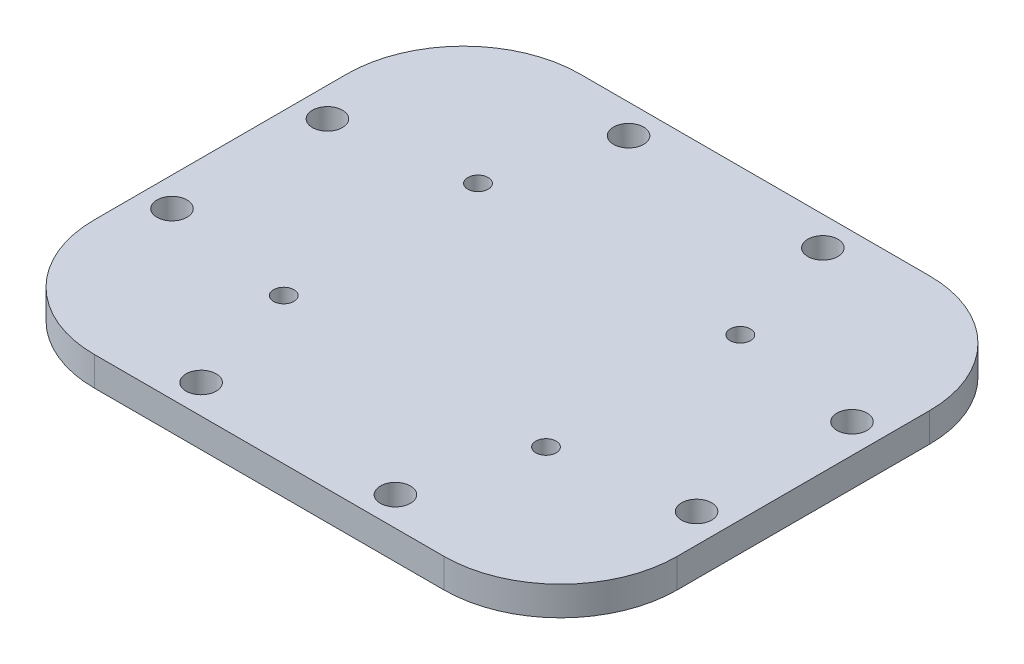
SolidWorks part; units mm, degrees
material "ABS"
ref_plane "前视基准面" through (0, 0, 0) normal (0, 0, 1) x (1, 0, 0)
ref_plane "上视基准面" through (0, 0, 0) normal (0, 1, 0) x (1, 0, 0)
ref_plane "右视基准面" through (0, 0, 0) normal (1, 0, 0) x (0, 0, -1)
other "Configuration Table"
sketch "草图1" plane through (0, 0, 0) normal (0, 1, 0) x (1, 0, 0)
  line L1 (-30, 25) -> (30, 25)
  line L2 (-30, 25) -> (-30, -25)
  line L3 (-30, -25) -> (30, -25)
  line L4 (30, 25) -> (30, -25)
  line L5 (-30, 25) -> (30, -25) construction
  line L6 (-30, -25) -> (30, 25) construction
  point P0 (0, 0)
  dimension "D1" = 60
  dimension "D2" = 50
extrude "凸台-拉伸1" add sketch "草图1" along normal blind 3
sketch "草图7" plane through (0, 3, 0) normal (0, 1, 0) x (1, 0, 0)
  line L0 (0, 0) -> (0, 25) construction
  line L1 (30, 25) -> (-30, 25) construction
  line L2 (0, 0) -> (30, 0) construction
  line L3 (30, -25) -> (30, 25) construction
  circle A0 centre (13.5, 10) radius 1.05
  circle A1 centre (-13.5, 10) radius 1.05
  circle A2 centre (-13.5, -10) radius 1.05
  circle A3 centre (13.5, -10) radius 1.05
  dimension "D1" = 2.1
  dimension "D2" = 20
  dimension "D3" = 27
extrude "切除-拉伸1" cut sketch "草图7" against normal blind 10
sketch "草图8" plane through (0, 0, 0) normal (0, -1, 0) x (1, 0, 0)
  line L0 (0, 25) -> (0, 0) construction
  line L1 (-30, 25) -> (30, 25) construction
  line L2 (0, 0) -> (30, 0) construction
  line L3 (30, 25) -> (30, -25) construction
  line L4 (-10, 22) -> (10, 22) construction
  circle A0 centre (27, 8) radius 1.55
  circle A1 centre (10, 22) radius 1.55
  circle A2 centre (-10, 22) radius 1.55
  circle A3 centre (-27, 8) radius 1.55
  circle A4 centre (-27, -8) radius 1.55
  circle A5 centre (-10, -22) radius 1.55
  circle A6 centre (10, -22) radius 1.55
  circle A7 centre (27, -8) radius 1.55
  dimension "D1" = 44
  dimension "D2" = 54
  dimension "D3" = 3.1
  dimension "D4" = 20
  dimension "D5" = 16
extrude "切除-拉伸2" cut sketch "草图8" against normal blind 10
fillet "圆角1" radius 12 4 edges at (30, 1.5, 25) (-30, 1.5, -25) (30, 1.5, -25) (-30, 1.5, 25)
